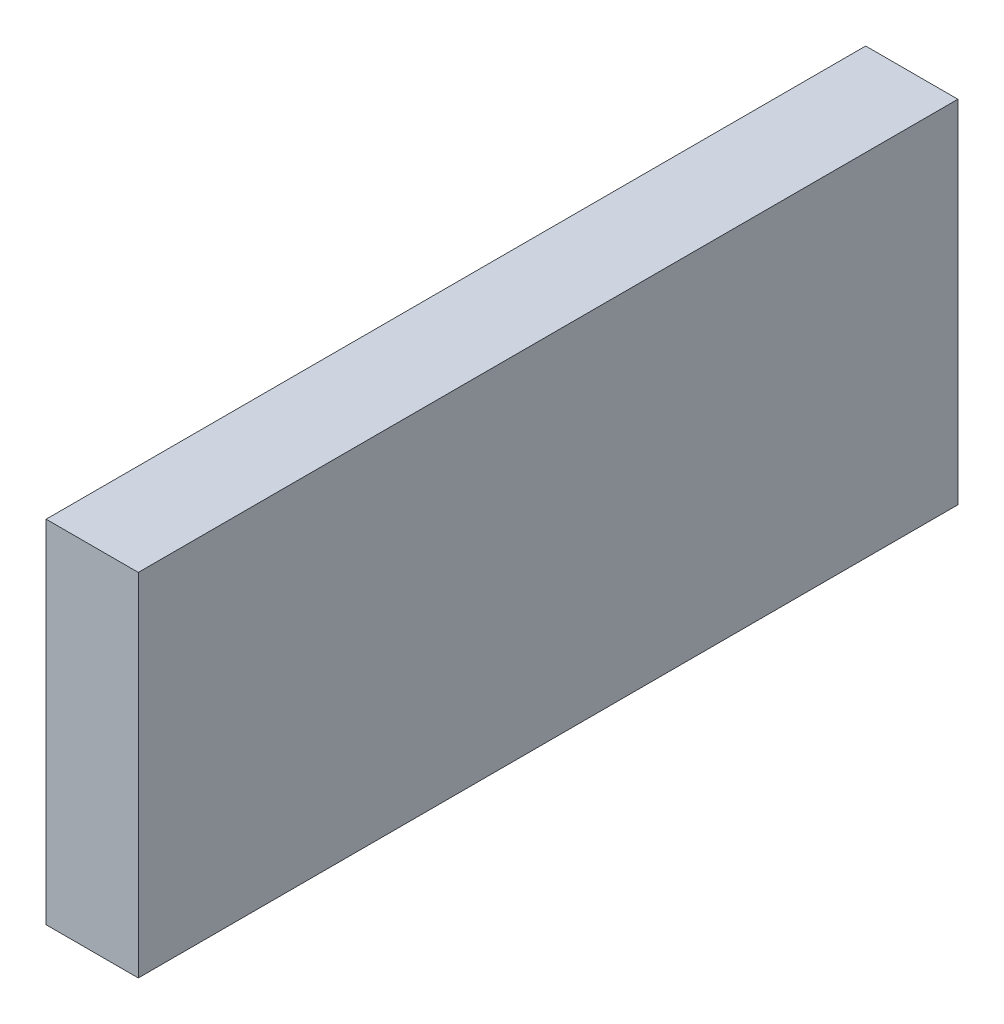
SolidWorks part; units mm, degrees
ref_plane "Front Plane" through (0, 0, 0) normal (0, 0, 1) x (1, 0, 0)
ref_plane "Top Plane" through (0, 0, 0) normal (0, 1, 0) x (1, 0, 0)
ref_plane "Right Plane" through (0, 0, 0) normal (1, 0, 0) x (0, 0, -1)
sketch "Sketch1" plane through (0, 0, 0) normal (1, 0, 0) x (0, 0, -1)
  line L0 (-44.45, 19.05) -> (44.45, -19.05) construction
  line L1 (-44.45, 19.05) -> (44.45, 19.05)
  line L2 (-44.45, 19.05) -> (-44.45, -19.05)
  line L3 (-44.45, -19.05) -> (44.45, -19.05)
  line L4 (44.45, 19.05) -> (44.45, -19.05)
  dimension "D1" = 88.9
  dimension "D2" = 38.1
extrude "Boss-Extrude1" add sketch "Sketch1" along normal blind 10
